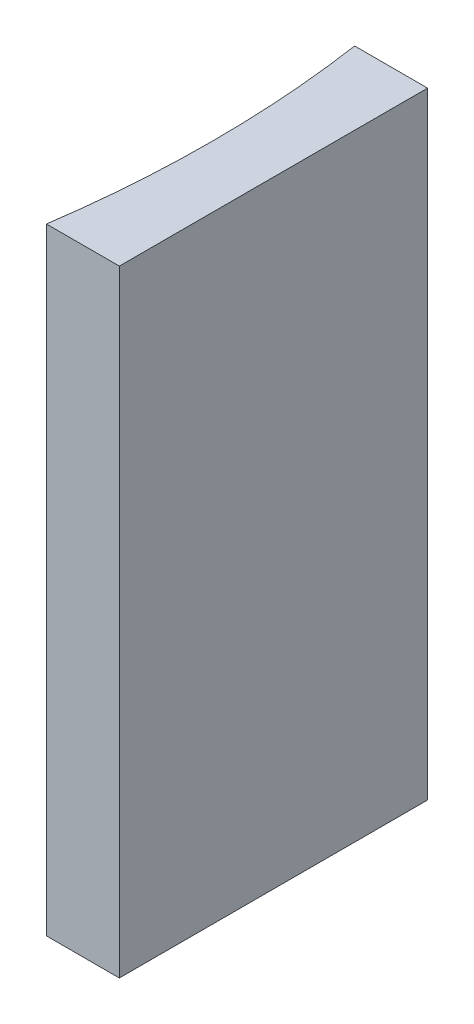
SolidWorks part; units mm, degrees
ref_plane "前视基准面" through (0, 0, 0) normal (0, 0, 1) x (1, 0, 0)
ref_plane "上视基准面" through (0, 0, 0) normal (0, 1, 0) x (1, 0, 0)
ref_plane "右视基准面" through (0, 0, 0) normal (1, 0, 0) x (0, 0, -1)
sketch "草图1" plane through (0, 0, 0) normal (0, 1, 0) x (1, 0, 0)
  line L0 (0, 0) -> (0, -10)
  line L1 (0, 0) -> (-2.3658, 0)
  line L2 (0, -10) -> (-2.3658, -10)
  line L3 (21.2259, -5) -> (-21.2259, -5) construction
  arc A0 (-2.3658, -10) -> (-2.3658, 0) centre (-36.35, -5) ccw
  point P7 (-2, -5)
  point P8 (0, -5)
  dimension "D2" = 34.35
  dimension "D3" = 2
  dimension "D1" = 10
extrude "凸台-拉伸1" add sketch "草图1" along normal blind 20
